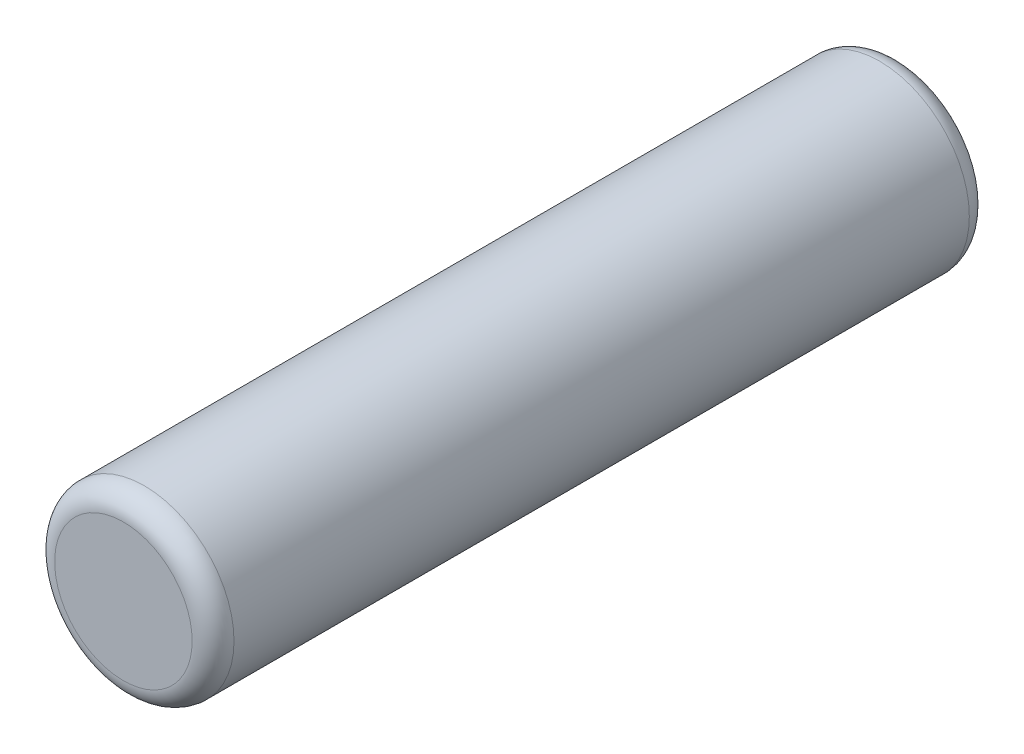
SolidWorks part; units mm, degrees
ref_plane "Front" through (0, 0, 0) normal (0, 0, 1) x (1, 0, 0)
ref_plane "Top" through (0, 0, 0) normal (0, 1, 0) x (1, 0, 0)
ref_plane "Right" through (0, 0, 0) normal (1, 0, 0) x (0, 0, -1)
sketch "Sketch1" plane through (0, 0, 0) normal (0, 0, 1) x (1, 0, 0)
  circle A0 centre (0, 0) radius 1.5
  dimension "D1" = 3
extrude "Boss-Extrude1" add sketch "Sketch1" along normal mid plane 13
fillet "Fillet1" radius 0.35 2 edges at (1.5, 0, -6.5) (1.5, 0, 6.5)
